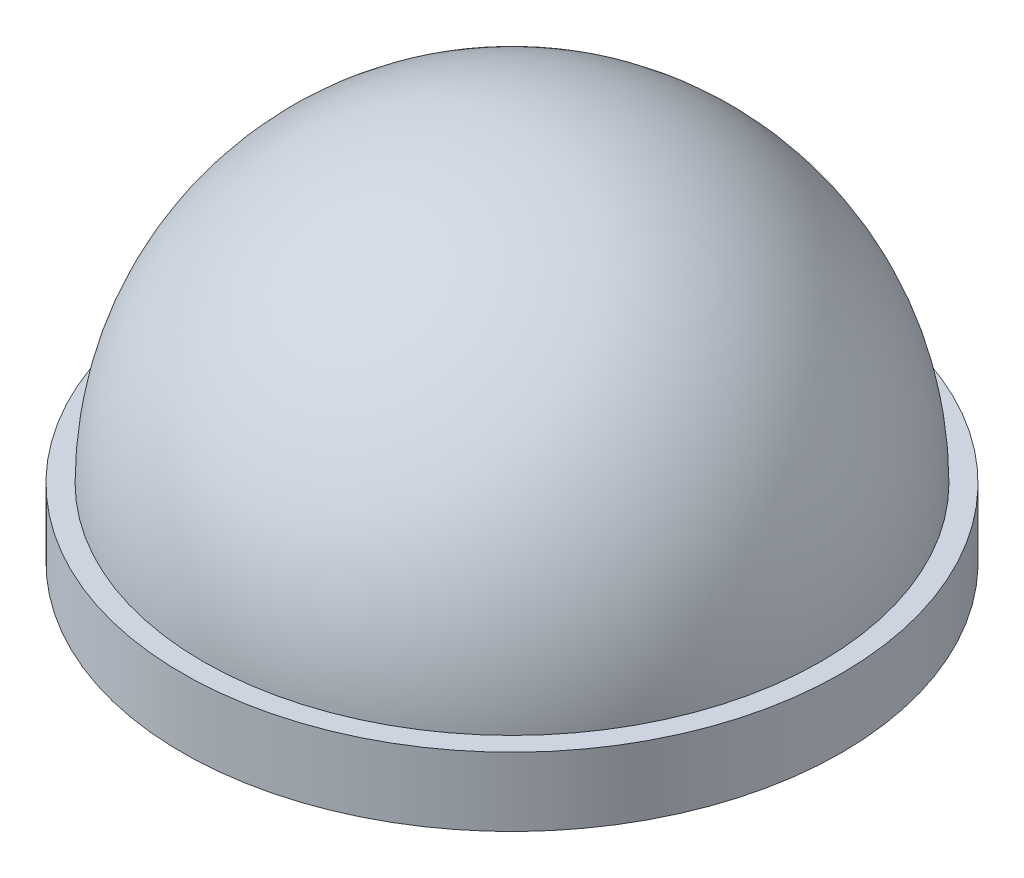
SolidWorks part; units mm, degrees
material "POLIURETANO (11671)"
ref_plane "Alzado" through (0, 0, 0) normal (0, 0, 1) x (1, 0, 0)
ref_plane "Planta" through (0, 0, 0) normal (0, 1, 0) x (1, 0, 0)
ref_plane "Vista lateral" through (0, 0, 0) normal (1, 0, 0) x (0, 0, -1)
sketch "Croquis1" plane through (0, 0, 0) normal (0, 0, 1) x (1, 0, 0)
  line L1 (0, 0) -> (-4.8, 0)
  line L2 (-4.8, 0) -> (-4.8, 1)
  line L3 (-4.8, 1) -> (-4.5, 1)
  line L4 (0, 5.5) -> (0, 0)
  arc A0 (0, 5.5) -> (-4.5, 1) centre (0, 1) ccw
  dimension "D1" = 4.5
revolve "Revolución1" add sketch "Croquis1" angle 360 about L4
